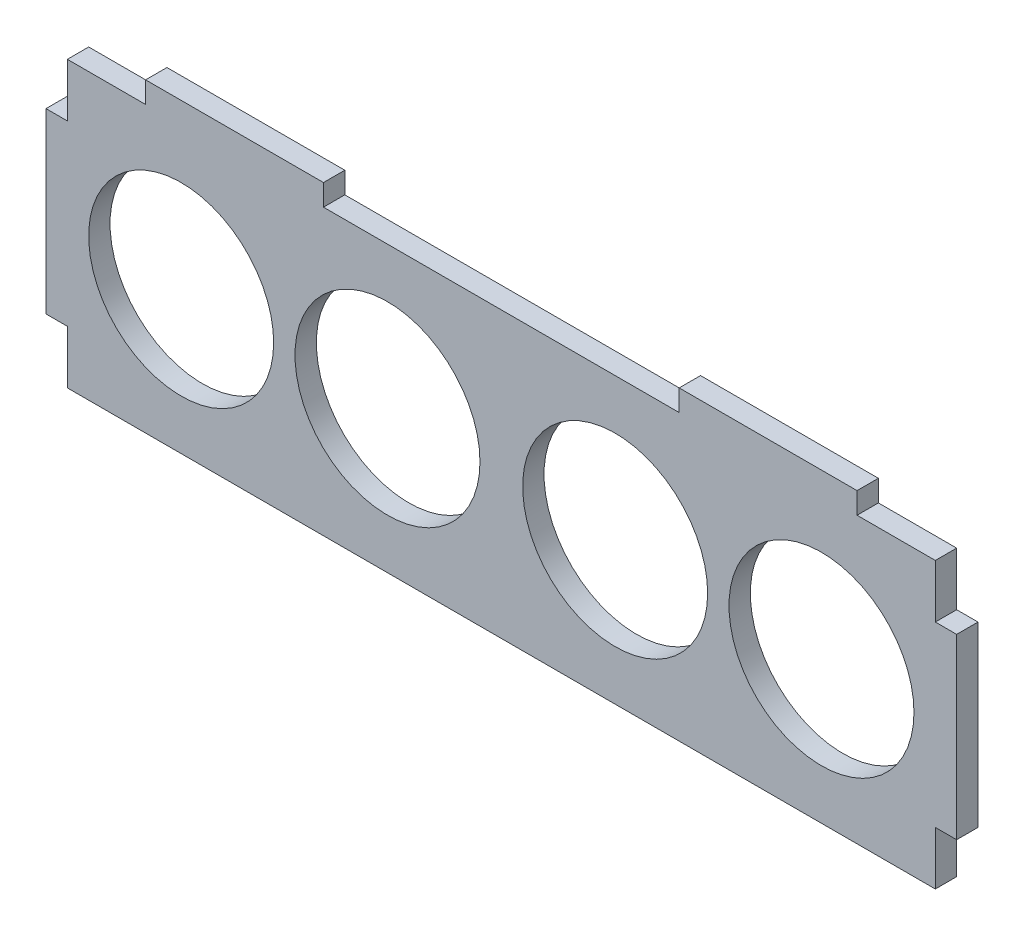
SolidWorks part; units mm, degrees
ref_plane "Front Plane" through (0, 0, 0) normal (0, 0, 1) x (1, 0, 0)
ref_plane "Top Plane" through (0, 0, 0) normal (0, 1, 0) x (1, 0, 0)
ref_plane "Right Plane" through (0, 0, 0) normal (1, 0, 0) x (0, 0, -1)
sketch "Sketch1" plane through (0, 0, 0) normal (0, 0, 1) x (1, 0, 0)
  line L0 (-64, 0) -> (64, 0) construction
  line L1 (-61, -20) -> (61, -20)
  line L2 (-61, -20) -> (-61, 20)
  line L3 (-61, 20) -> (61, 20)
  line L4 (61, -20) -> (61, 20)
  line L5 (-61, -20) -> (61, 20) construction
  line L6 (-61, 20) -> (61, -20) construction
  line L7 (-61, 12.5) -> (-64, 12.5)
  line L8 (-61, 12.5) -> (-61, -12.5)
  line L9 (-61, -12.5) -> (-64, -12.5)
  line L10 (-64, 12.5) -> (-64, -12.5)
  line L11 (61, 12.5) -> (64, 12.5)
  line L12 (61, 12.5) -> (61, -12.5)
  line L13 (61, -12.5) -> (64, -12.5)
  line L14 (64, 12.5) -> (64, -12.5)
  line L15 (-50, 20) -> (-25, 20)
  line L16 (-50, 20) -> (-50, 23)
  line L17 (-50, 23) -> (-25, 23)
  line L18 (-25, 20) -> (-25, 23)
  line L19 (25, 20) -> (50, 20)
  line L20 (25, 20) -> (25, 23)
  line L21 (25, 23) -> (50, 23)
  line L22 (50, 20) -> (50, 23)
  circle A0 centre (-45, 0) radius 13
  circle A1 centre (45, 0) radius 13
  circle A2 centre (-16, 0) radius 13
  circle A3 centre (16, 0) radius 13
  point P0 (0, 0)
  point P21 (-64, 0)
  point P22 (64, 0)
  dimension "D5" = 26
  dimension "D1" = 25
  dimension "D2" = 3
  dimension "D3" = 25
  dimension "D4" = 25
  dimension "D6" = 16
  dimension "D7" = 16
  dimension "D8" = 122
  dimension "D9" = 40
  dimension "D10" = 45
  dimension "D11" = 45
extrude "Boss-Extrude1" add sketch "Sketch1" along normal blind 3 contours L7 L10 L9 L2 | L3 L18 L17 L16 | L3 L22 L21 L20 | L14 L11 L4 L13 | L1 L4 L3 L2 A3 A2 A1 A0
